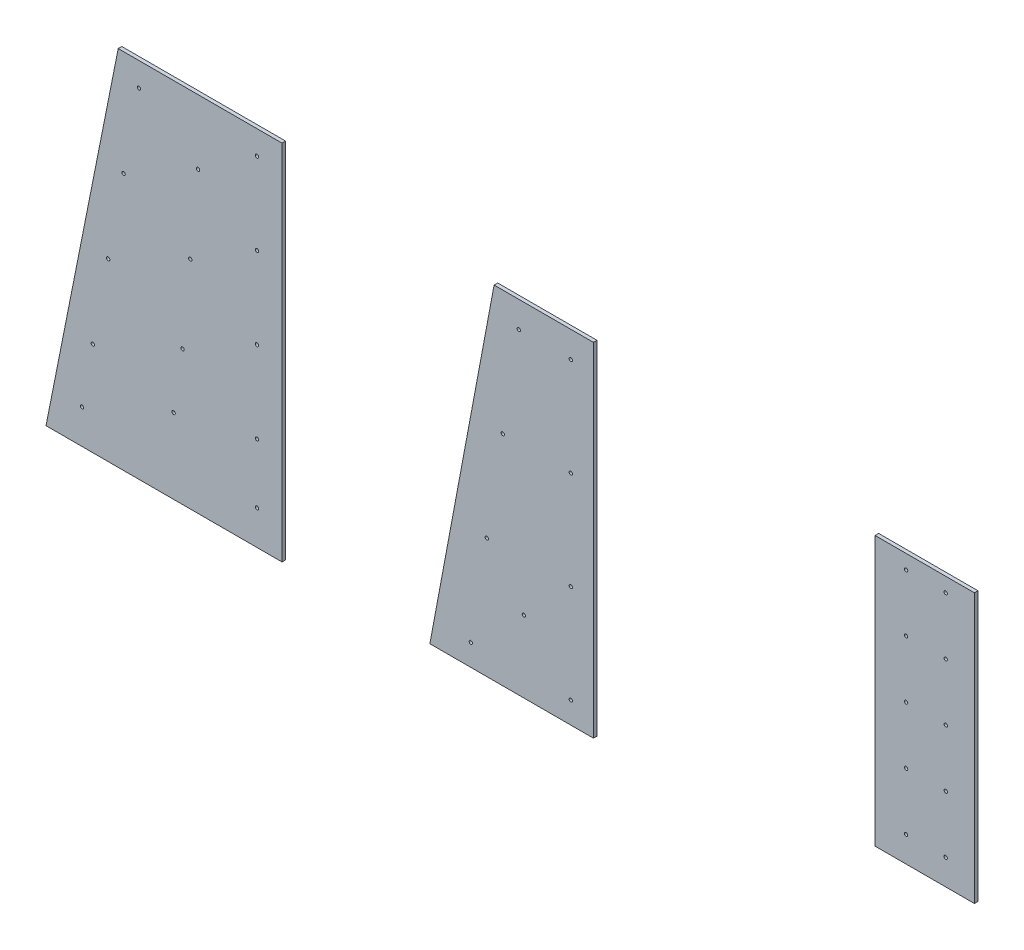
SolidWorks part; units mm, degrees
ref_plane "Ön Düzlem" through (0, 0, 0) normal (0, 0, 1) x (1, 0, 0)
ref_plane "Üst Düzlem" through (0, 0, 0) normal (0, 1, 0) x (1, 0, 0)
ref_plane "Sağ Düzlem" through (0, 0, 0) normal (1, 0, 0) x (0, 0, -1)
sketch "Çizim1" plane through (0, 0, 0) normal (0, 0, 1) x (1, 0, 0)
  line L0 (-17083.8906, -24311.5862) -> (-17770.3778, -24311.5862)
  line L1 (-17770.3778, -24311.5862) -> (-18072.9723, -25831.5862)
  line L2 (-18072.9723, -25831.5862) -> (-17083.8906, -25831.5862)
  line L3 (-17083.8906, -25831.5862) -> (-17083.8906, -24311.5862)
  line L4 (-16464.4629, -25818.5904) -> (-16195.3466, -24382.2291)
  line L5 (-15779.113, -25818.5904) -> (-16464.4629, -25818.5904)
  line L6 (-15779.113, -24382.1443) -> (-15779.113, -25818.5904)
  line L7 (-16195.3466, -24382.2291) -> (-15779.113, -24382.1443)
  line L8 (-14599.0053, -24492.8814) -> (-14598.9343, -25620.3816) construction
  line L9 (-14182.7429, -24492.8559) -> (-14182.6723, -25620.3561)
  line L10 (-14182.7429, -24492.8559) -> (-14599.0053, -24492.8814)
  line L11 (-14182.6723, -25620.3561) -> (-14598.9343, -25620.3823) construction
  line L12 (-14599.0053, -24492.8814) -> (-14598.9343, -25620.3816)
  line L13 (-14598.9343, -25620.3816) -> (-14182.6723, -25620.3561)
  circle A0 centre (-17747.8076, -24753.6011) radius 7
  circle A1 centre (-17812.4956, -25095.616) radius 7
  circle A2 centre (-17877.1837, -25437.6309) radius 7
  circle A3 centre (-17436.0051, -24582.5937) radius 7
  circle A4 centre (-17188.8906, -24753.6011) radius 7
  circle A5 centre (-17188.8906, -25095.616) radius 7
  circle A6 centre (-17188.8906, -25437.6309) radius 7
  circle A7 centre (-17683.1196, -24411.5862) radius 7
  circle A8 centre (-17468.3491, -24924.6086) radius 7
  circle A9 centre (-17500.6931, -25266.6235) radius 7
  circle A10 centre (-17188.8906, -24411.5862) radius 7
  circle A11 centre (-16158.9229, -24904.033) radius 7
  circle A12 centre (-16225.9203, -25315.9218) radius 7
  circle A13 centre (-16292.9176, -25727.8105) radius 7
  circle A14 centre (-15874.113, -25727.8105) radius 7
  circle A15 centre (-15874.113, -25315.9218) radius 7
  circle A16 centre (-15874.113, -24904.033) radius 7
  circle A17 centre (-16091.9255, -24492.1443) radius 7
  circle A18 centre (-15874.113, -24492.1443) radius 7
  circle A19 centre (-14469.0053, -24552.8814) radius 7
  circle A20 centre (-14302.7429, -24552.8814) radius 7
  circle A21 centre (-14469.0053, -24792.8814) radius 7
  circle A22 centre (-14302.7429, -24792.8814) radius 7
  circle A23 centre (-14469.0053, -25032.8814) radius 7
  circle A24 centre (-14302.7429, -25032.8814) radius 7
  circle A25 centre (-14469.0053, -25272.8814) radius 7
  circle A26 centre (-14302.7429, -25272.8814) radius 7
  circle A27 centre (-14469.0053, -25512.8814) radius 7
  circle A28 centre (-14302.7429, -25512.8814) radius 7
  circle A29 centre (-16070.5459, -25517.7467) radius 7
  circle A30 centre (-17922.3004, -25687.6309) radius 7
  circle A31 centre (-17188.8906, -25687.6309) radius 7
  circle A32 centre (-17538.1201, -25516.6235) radius 7
  dimension "D3" = 14
  dimension "D24" = 14
  dimension "D31" = 291.4329
  dimension "D1" = 1520
  dimension "D2" = 989.0817
  dimension "D4" = 686.4871
  dimension "D5" = 250
  dimension "D6" = 342.0149
  dimension "D7" = 342.0149
  dimension "D8" = 342.0149
  dimension "D9" = 143.9553
  dimension "D10" = 352.1145
  dimension "D11" = 384.4585
  dimension "D12" = 416.8025
  dimension "D13" = 454.2295
  dimension "D14" = 599.229
  dimension "D15" = 663.917
  dimension "D16" = 728.605
  dimension "D17" = 793.293
  dimension "D18" = 838.4098
  dimension "D19" = 105
  dimension "D20" = 1436.4461
  dimension "D21" = 685.3498
  dimension "D22" = 416.2335
  dimension "D23" = 95
  dimension "D25" = 95
  dimension "D26" = 300.8437
  dimension "D27" = 90.7799
  dimension "D28" = 502.6687
  dimension "D29" = 914.5574
  dimension "D30" = 1326.4461
  dimension "D32" = 312.8125
  dimension "D33" = 379.8099
  dimension "D34" = 446.8072
  dimension "D35" = 513.8046
  dimension "D37" = 166.2625
  dimension "D38" = 129.9811
  dimension "D39" = 107.4822
  dimension "D40" = 347.4822
  dimension "D41" = 587.4822
  dimension "D42" = 827.4822
  dimension "D43" = 1067.4822
  dimension "D44" = 1127.5002
extrude "Yükseklik-Ekstrüzyon1" add sketch "Çizim1" along normal blind 15
